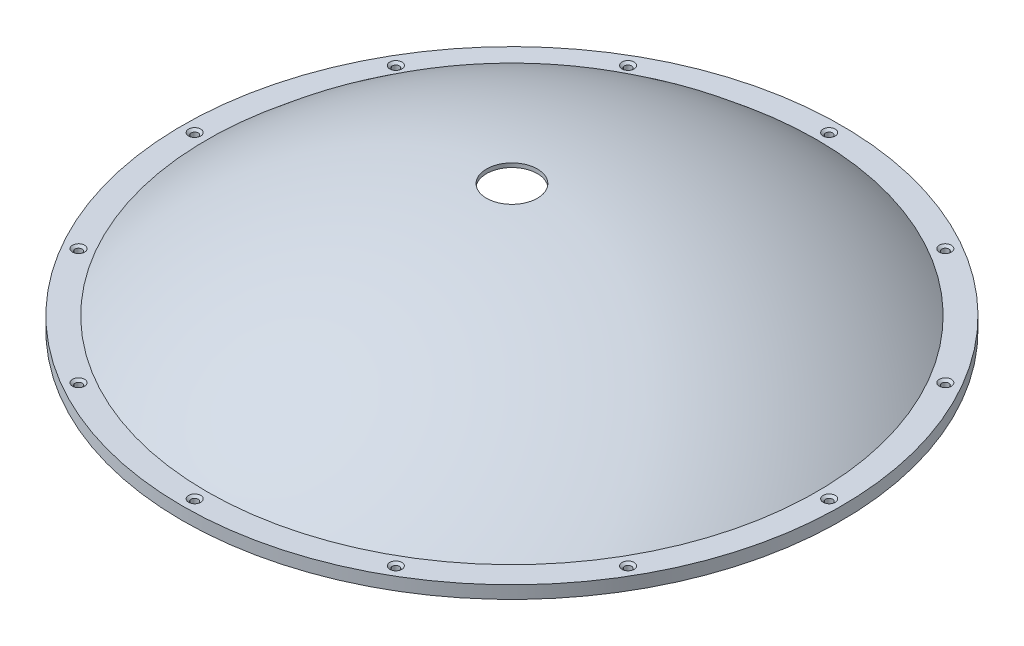
SolidWorks part; units mm, degrees
material "6063-T6"
ref_plane "Front Plane" through (0, 0, 0) normal (0, 0, 1) x (1, 0, 0)
ref_plane "Top Plane" through (0, 0, 0) normal (0, 1, 0) x (1, 0, 0)
ref_plane "Right Plane" through (0, 0, 0) normal (1, 0, 0) x (0, 0, -1)
ref_axis "Axis1" through (0, 55, 0) along (0, -1, 0)
sketch "Sketch1" plane through (0, 0, 0) normal (0, 0, 1) x (1, 0, 0)
  line L0 (-82.3595, 0) -> (-76.2, 0)
  line L1 (0, 55) -> (0, -55) construction
  line L2 (-82.3595, 0) -> (-82.3595, 3.175)
  line L3 (-82.3595, 3.175) -> (-76.2, 3.175)
  line L4 (-76.2, 0) -> (-76.2, -9.1451) construction
  line L5 (-6.35, 31.7635) -> (-6.35, 30.7459)
  line L6 (-76.2, 0) -> (0, 0) construction
  arc A0 (-74.8116, 3.0384) -> (-76.2, 0) centre (-72.1811, 0) ccw
  arc A1 (-74.8116, 3.0384) -> (-6.35, 30.7459) centre (0, -83.3775) cw
  arc A2 (-76.2, 3.175) -> (-6.35, 31.7635) centre (0, -83.3775) cw
  point P13 (0, 0)
  dimension "D1" = 3.175
  dimension "D2" = 6.1595
  dimension "D3" = 114.3
  dimension "D4" = 6.35
  dimension "D5" = 1.016
  dimension "D6" = 76.2
revolve "Revolve1" add sketch "Sketch1" angle 360 about axis through (0, 55, 0) along (0, -1, 0)
ref_plane "Hole Location Plane" through (0, 3.175, 0) normal (0, 1, 0) x (1, 0, 0)
sketch "Hole Location" plane through (0, 3.175, 0) normal (0, 1, 0) x (1, 0, 0)
  line L0 (0, 0) -> (-79.2797, 0) construction
  circle A0 centre (0, 0) radius 79.2797 construction
  dimension "D1" = 158.5595
hole_wizard "CSK for #0 Flat Head Machine Screw (100)1" positions "Sketch4" profile "Sketch5" countersink size "#0" standard "ANSI Inch" end condition through all
sketch "Sketch4" plane through (0, 3.175, 0) normal (0, 1, 0) x (1, 0, 0)
  point P0 (-79.2797, 0)
sketch "Sketch5" plane through (-79.2797, 3.175, 0) normal (1, 0, 0) x (0, 0, 1)
  line L0 (0, 0) -> (0, 3.175)
  line L1 (0, 3.175) -> (0.889, 3.175)
  line L2 (0.889, 3.175) -> (0.889, 0.5222)
  line L3 (0.889, 0.5222) -> (1.5113, 0)
  line L5 (1.5113, 0) -> (0, 0)
  line L6 (-0.889, 0.5222) -> (-1.5113, 0) construction
  line L11 (0, -6.35) -> (0, 107.95) construction
  dimension "Thru Hole Dia." = 1.778
  dimension "Thru Hole Depth" = 3.175
  dimension "Near C'Sink Dia." = 3.0226
  dimension "Near C'Sink Angle" = 100
pattern_circular "CirPattern1" count 12 every 30 about axis through (0, 0, 0) along (0, 1, 0) of "CSK for #0 Flat Head Machine Screw (100)1"
